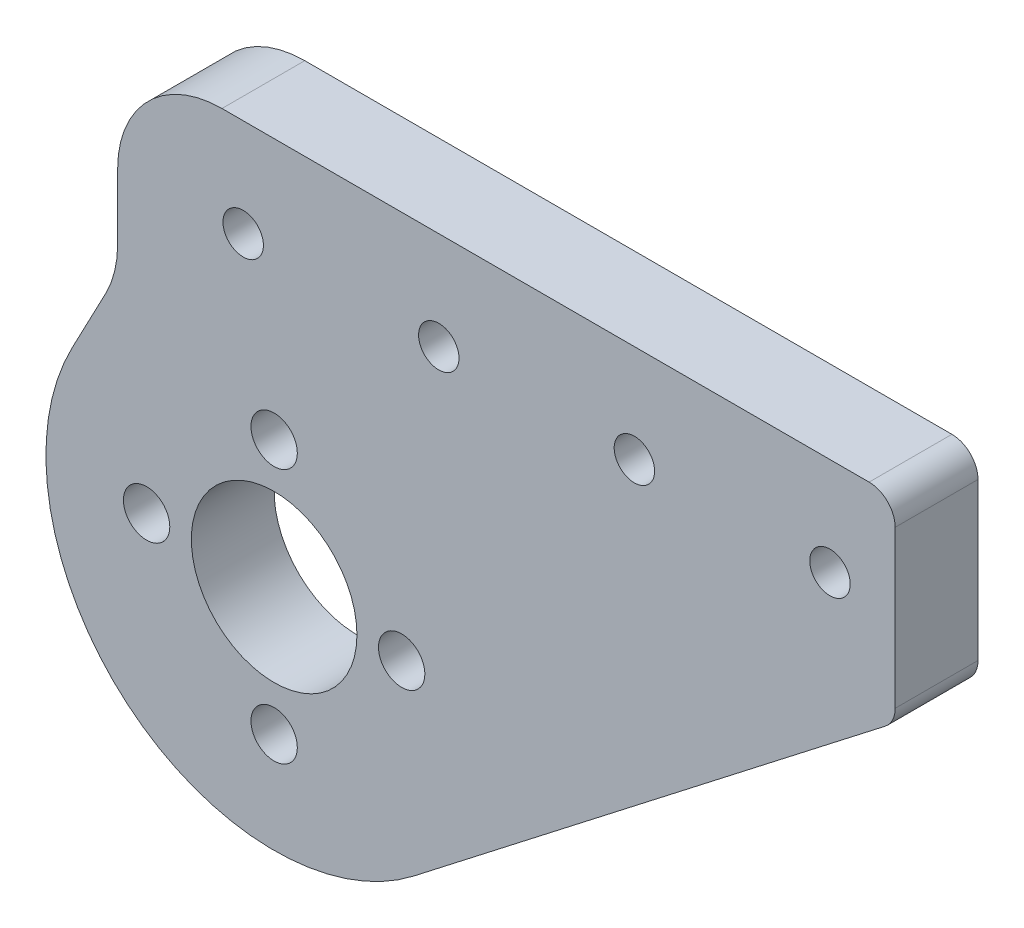
SolidWorks part; units mm, degrees
ref_plane "Front Plane" through (0, 0, 0) normal (0, 0, 1) x (1, 0, 0)
ref_plane "Top Plane" through (0, 0, 0) normal (0, 1, 0) x (1, 0, 0)
ref_plane "Right Plane" through (0, 0, 0) normal (1, 0, 0) x (0, 0, -1)
sketch "Sketch1" plane through (0, 0, 0) normal (0, 0, 1) x (1, 0, 0)
  line L12 (-6.7375, 29.779) -> (47.6261, 29.779)
  line L13 (10.3761, 14.779) -> (47.6261, 14.779)
  line L16 (47.6261, 14.779) -> (47.6261, 29.779)
  line L19 (-6.7375, 29.779) -> (-12, 29.779)
  line L21 (-12, 29.779) -> (-12, 14.779)
  line L22 (-12, 14.779) -> (-15.4886, 8.1458)
  line L23 (10.3761, 14.779) -> (7.3627, 14.779)
  line L24 (47.6261, 14.779) -> (10.7221, -13.8306)
  circle A0 centre (0, 0) radius 6.35
  circle A1 centre (-2.3739, 22.279) radius 1.55
  circle A2 centre (12.6261, 22.279) radius 1.55
  circle A3 centre (27.6261, 22.279) radius 1.55
  circle A4 centre (42.6261, 22.279) radius 1.55
  circle A8 centre (0, 0) radius 9.779
  circle A9 centre (0, 9.779) radius 1.778
  circle A10 centre (9.779, 0) radius 1.778
  circle A11 centre (0, -9.779) radius 1.778
  circle A12 centre (-9.779, 0) radius 1.778
  circle A14 centre (0, 0) radius 17.5
  point P21 (0, 0)
  dimension "D4" = 3.1
  dimension "D5" = 4
  dimension "D6" = 3.556
  dimension "D2" = 12
  dimension "D1" = 12.7
  dimension "D3" = 19.558
  dimension "D9" = 5
  dimension "D11" = 35
  dimension "D12" = 15
  dimension "D13" = 5
  dimension "D14" = 15
  dimension "D7" = 4
extrude "Boss-Extrude1" add sketch "Sketch1" along normal blind 6.35
fillet "Fillet2" radius 2 2 edges at (47.6261, 29.779, 3.175) (47.6261, 14.779, 3.175)
fillet "Fillet4" radius 8 2 edges at (-12, 29.779, 3.175) (-12, 14.779, 3.175)
